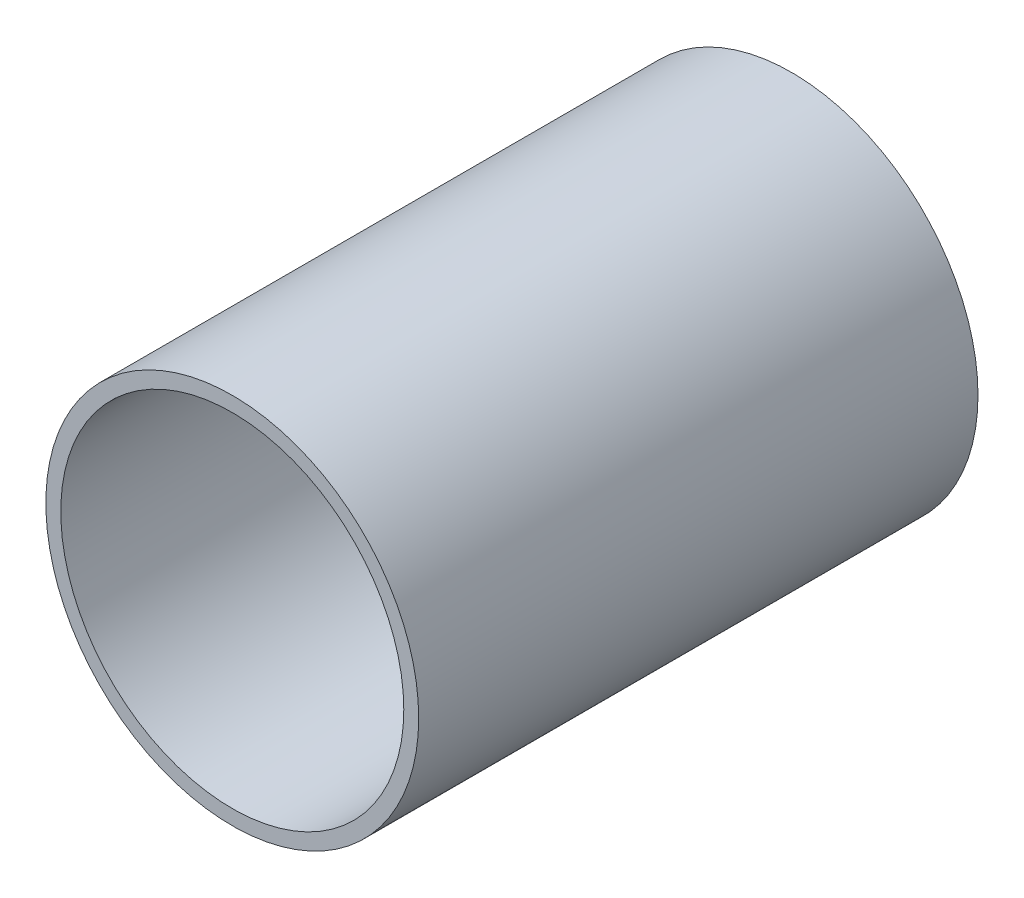
SolidWorks part; units mm, degrees
ref_plane "Front Plane" through (0, 0, 0) normal (0, 0, 1) x (1, 0, 0)
ref_plane "Top Plane" through (0, 0, 0) normal (0, 1, 0) x (1, 0, 0)
ref_plane "Right Plane" through (0, 0, 0) normal (1, 0, 0) x (0, 0, -1)
sketch "Sketch1" plane through (0, 0, 0) normal (0, 0, 1) x (1, 0, 0)
  circle A0 centre (0, 0) radius 10
extrude "Boss-Extrude1" add sketch "Sketch1" along normal blind 30
sketch "Sketch2" plane through (0, 0, 0) normal (0, 0, 1) x (1, 0, 0)
  circle A0 centre (0, 0) radius 2.5
extrude "Boss-Extrude3" add sketch "Sketch2" against normal blind 2
shell "Shell1" thickness 0.8
sketch "Sketch3" plane through (0, 0, 0) normal (0, 0, 1) x (1, 0, 0)
  circle A0 centre (5, 0) radius 0.5
  circle A1 centre (0, -5) radius 0.5
  circle A2 centre (-5, 0) radius 0.5
  circle A3 centre (0, 5) radius 0.5
  point P12 (0, 0)
  dimension "D1" = 5
  dimension "D2" = 4
extrude "Cut-Extrude2" cut sketch "Sketch3" against normal through all both and the other way through all
